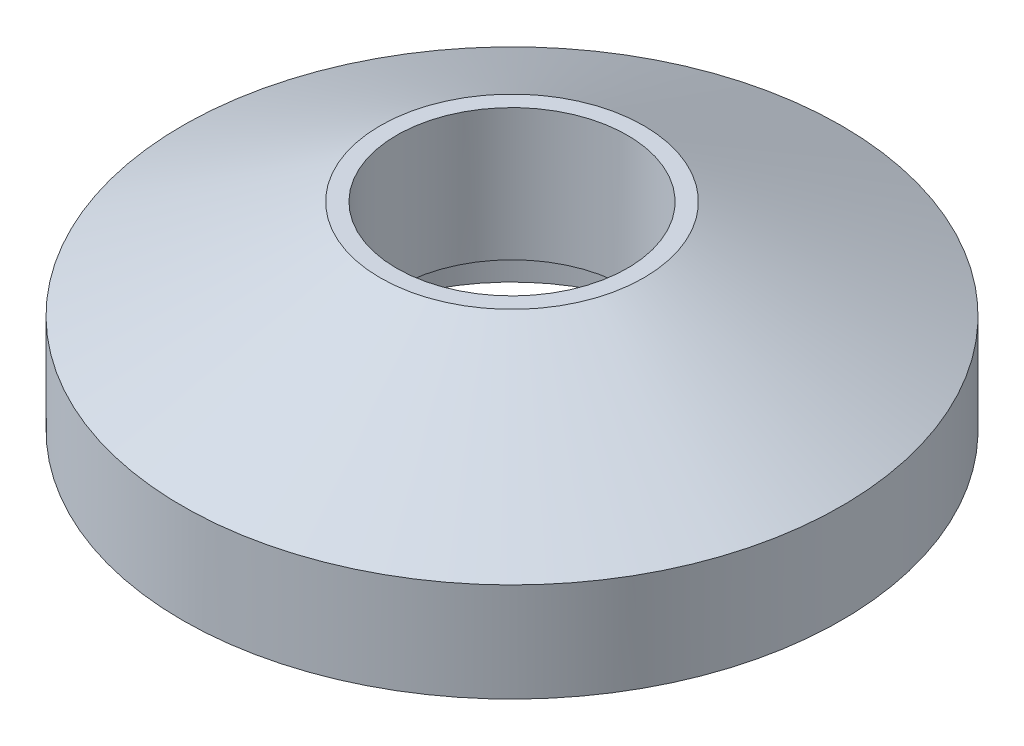
SolidWorks part; units mm, degrees
ref_plane "Alzado" through (0, 0, 0) normal (0, 0, 1) x (1, 0, 0)
ref_plane "Planta" through (0, 0, 0) normal (0, 1, 0) x (1, 0, 0)
ref_plane "Vista lateral" through (0, 0, 0) normal (1, 0, 0) x (0, 0, -1)
sketch "Croquis1" plane through (0, 0, 0) normal (0, 1, 0) x (1, 0, 0)
  circle A0 centre (0, 0) radius 50
  dimension "D1" = 100
extrude "Saliente-Extruir1" add sketch "Croquis1" along normal blind 15
ref_plane "Plano1" through (0, 30, 0) normal (0, 1, 0) x (1, 0, 0)
sketch "Croquis3" plane through (0, 30, 0) normal (0, 1, 0) x (1, 0, 0)
  circle A0 centre (0, 0) radius 20
  dimension "D1" = 40
loft "Recubrir1" add profiles "Croquis3" section "Croquis3" section edge at (0, 15, 50)
sketch "Croquis4" plane through (0, 30, 0) normal (0, 1, 0) x (1, 0, 0)
  circle A0 centre (0, 0) radius 17.5
  dimension "D1" = 35
extrude "Cortar-Extruir1" cut sketch "Croquis4" against normal through all
sketch "Croquis5" plane through (0, 0, 0) normal (0, -1, 0) x (1, 0, 0)
  circle A0 centre (0, 0) radius 27.5
  dimension "D1" = 55
extrude "Cortar-Extruir2" cut sketch "Croquis5" against normal blind 10
